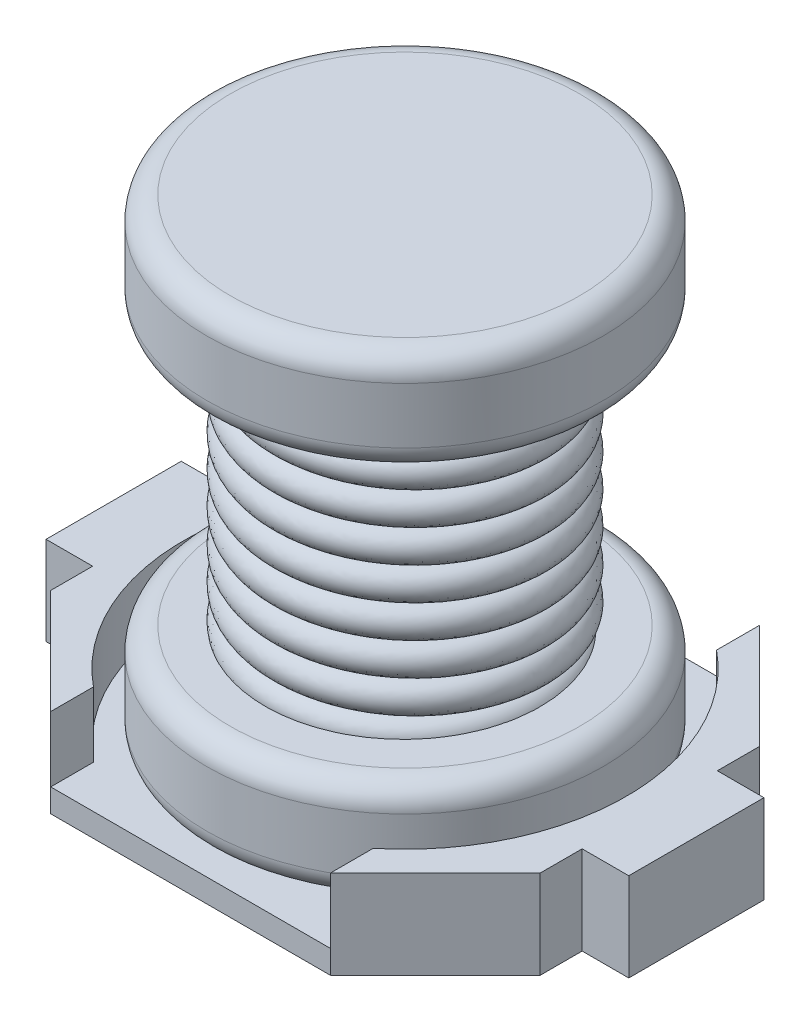
SolidWorks part; units mm, degrees
ref_plane "Alzado" through (0, 0, 0) normal (0, 0, 1) x (1, 0, 0)
ref_plane "Planta" through (0, 0, 0) normal (0, 1, 0) x (1, 0, 0)
ref_plane "Vista lateral" through (0, 0, 0) normal (1, 0, 0) x (0, 0, -1)
sketch "Croquis1" plane through (0, 0, 0) normal (0, 1, 0) x (1, 0, 0)
  line L1 (-5.25, 4.6) -> (5.25, 4.6)
  line L2 (-5.25, 4.6) -> (-5.25, -4.6)
  line L3 (-5.25, -4.6) -> (5.25, -4.6)
  line L4 (5.25, 4.6) -> (5.25, -4.6)
  dimension "D1" = 10.5
  dimension "D2" = 9.2
  dimension "D3" = 5.25
  dimension "D4" = 4.6
extrude "Extruir1" add sketch "Croquis1" along normal blind 1.9
sketch "Croquis2" plane through (0, 0, 4.6) normal (0, 0, 1) x (1, 0, 0)
  line L0 (-5.25, 1.9) -> (5.25, 1.9) construction
  line L1 (-3, 1.9) -> (3, 1.9)
  line L2 (-3, 1.9) -> (-3, 0.5)
  line L3 (-3, 0.5) -> (3, 0.5)
  line L4 (3, 1.9) -> (3, 0.5)
  line L5 (-5.25, 0) -> (5.25, 0) construction
  point P6 (0, 0)
  dimension "D1" = 1.4
  dimension "D2" = 6
  dimension "D3" = 3
extrude "Cortar-Extruir1" cut sketch "Croquis2" against normal blind 13.9
sketch "Croquis3" plane through (0, 1.9, 0) normal (0, 1, 0) x (1, 0, 0)
  line L0 (5.25, -4.6) -> (5.25, 4.6) construction
  line L1 (5.25, 1.45) -> (6.25, 1.45)
  line L2 (5.25, 1.45) -> (5.25, -1.45)
  line L3 (5.25, -1.45) -> (6.25, -1.45)
  line L4 (6.25, 1.45) -> (6.25, -1.45)
  line L5 (0, 0) -> (0, 6.7938) construction
  line L6 (-6.25, 1.45) -> (-6.25, -1.45)
  line L7 (-5.25, -1.45) -> (-6.25, -1.45)
  line L8 (-5.25, 1.45) -> (-5.25, -1.45)
  line L9 (-5.25, 1.45) -> (-6.25, 1.45)
  dimension "D1" = 2.9
  dimension "D2" = 6.25
  dimension "D3" = 1.45
extrude "Extruir2" add sketch "Croquis3" against normal blind 1.9
sketch "Croquis4" plane through (0, 1.9, 0) normal (0, 1, 0) x (1, 0, 0)
  line L0 (-3, 4.6) -> (-5.25, 2.35)
  line L1 (-5.25, 4.6) -> (-5.25, 1.45) construction
  line L2 (-5.25, 2.35) -> (-6.1615, 2.35)
  line L3 (-6.1615, 2.35) -> (-6.1615, 5.0648)
  line L4 (-6.1615, 5.0648) -> (-3, 5.0648)
  line L5 (-3, 5.0648) -> (-3, 4.6)
  line L6 (-3, 4.6) -> (-5.25, 4.6) construction
  line L7 (0, 0) -> (0, 6.2441) construction
  line L8 (3, 5.0648) -> (3, 4.6)
  line L9 (6.1615, 5.0648) -> (3, 5.0648)
  line L10 (6.1615, 2.35) -> (6.1615, 5.0648)
  line L11 (5.25, 2.35) -> (6.1615, 2.35)
  line L12 (3, 4.6) -> (5.25, 2.35)
  line L13 (0, 0) -> (8.8726, 0) construction
  line L14 (3, -4.6) -> (5.25, -2.35)
  line L15 (5.25, -2.35) -> (6.1615, -2.35)
  line L16 (6.1615, -2.35) -> (6.1615, -5.0648)
  line L17 (6.1615, -5.0648) -> (3, -5.0648)
  line L18 (3, -5.0648) -> (3, -4.6)
  line L19 (-3, -5.0648) -> (-3, -4.6)
  line L20 (-6.1615, -5.0648) -> (-3, -5.0648)
  line L21 (-6.1615, -2.35) -> (-6.1615, -5.0648)
  line L22 (-5.25, -2.35) -> (-6.1615, -2.35)
  line L23 (-3, -4.6) -> (-5.25, -2.35)
  dimension "D1" = 45
extrude "Cortar-Extruir2" cut sketch "Croquis4" against normal blind 4.9
sketch "Croquis5" plane through (0, 0.5, 0) normal (0, 1, 0) x (1, 0, 0)
  circle A0 centre (0, 0) radius 4.75
  dimension "D1" = 9.5
extrude "Cortar-Extruir4" cut sketch "Croquis5" along normal blind 4.9
sketch "Croquis6" plane through (0, 0, 0) normal (1, 0, 0) x (0, 0, -1)
  line L0 (0, 0.5) -> (0, 10.7)
  line L1 (3.6827, 0.5) -> (-3.6827, 0.5) construction
  line L2 (0, 10.7) -> (4.25, 10.7)
  line L3 (4.25, 10.7) -> (4.25, 8.5)
  line L4 (4.25, 8.5) -> (2.25, 8.5)
  line L5 (2.25, 8.5) -> (2.25, 2.7)
  line L6 (2.25, 2.7) -> (4.25, 2.7)
  line L7 (4.25, 2.7) -> (4.25, 0.5)
  line L8 (4.25, 0.5) -> (0, 0.5)
  line L9 (4.6, 1.9) -> (2.35, 1.9) construction
  line L10 (0, 0.5) -> (0, -1.1025) construction
  dimension "D1" = 4.25
  dimension "D2" = 2.2
  dimension "D3" = 2.2
  dimension "D4" = 8.8
  dimension "D5" = 2.25
revolve "Revolución1" add sketch "Croquis6" angle 360 about L10
sketch "Croquis8" plane through (0, 0, 0) normal (1, 0, 0) x (0, 0, -1)
  circle A0 centre (2.6617, 3.06) radius 0.3421
sketch "Croquis9" plane through (0, 2.7, 0) normal (0, 1, 0) x (1, 0, 0)
  circle A0 centre (0, 0) radius 2.759
curve "Hélice/Espiral1" pitch 0.7 height 5.6 turns 8
sweep "Barrer1" add profiles "Croquis8" path "Hélice/Espiral1"
fillet "Redondeo1" radius 0.5 4 edges at (0, 0.5, 4.25) (0, 2.7, 4.25) (0, 8.5, 4.25) (0, 10.7, 4.25)
